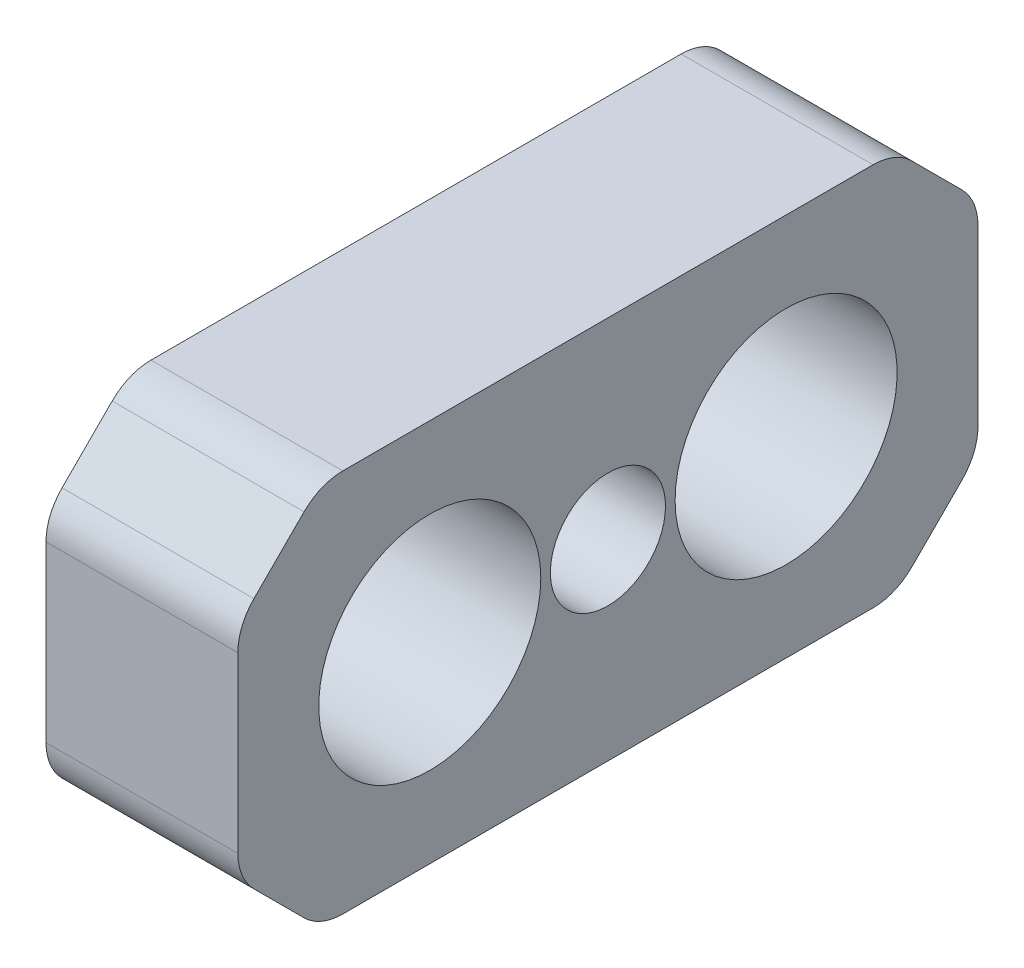
SolidWorks part; units mm, degrees
material "POM Acetal Copolymer"
ref_plane "Front Plane" through (0, 0, 0) normal (0, 0, 1) x (1, 0, 0)
ref_plane "Top Plane" through (0, 0, 0) normal (0, 1, 0) x (1, 0, 0)
ref_plane "Right Plane" through (0, 0, 0) normal (1, 0, 0) x (0, 0, -1)
sketch "Sketch1" plane through (0, 0, 0) normal (1, 0, 0) x (0, 0, -1)
  line L0 (0, 0) -> (0, -17.866) construction
  line L2 (13.5, -7) -> (-13.5, -7)
  line L3 (13.5, -7) -> (13.5, 7)
  line L4 (13.5, 7) -> (-13.5, 7)
  line L5 (-13.5, -7) -> (-13.5, 7)
  line L6 (13.5, -7) -> (-13.5, 7) construction
  line L7 (13.5, 7) -> (-13.5, -7) construction
  circle A0 centre (-6.5, 0) radius 4.05
  circle A1 centre (6.5, 0) radius 4.05
  dimension "D1" = 8.1
  dimension "D2" = 13
  dimension "D3" = 7
  dimension "D4" = 7
extrude "Boss-Extrude1" add sketch "Sketch1" along normal blind 7
fillet "Fillet1" [suppressed] radius 7
sketch "Sketch2" plane through (7, 0, 0) normal (1, 0, 0) x (0, 0, -1)
  line L1 (8.1781, -1) -> (-8.1781, -1)
  line L2 (8.1781, -1) -> (8.1781, 1)
  line L3 (8.1781, 1) -> (-8.1781, 1)
  line L4 (-8.1781, -1) -> (-8.1781, 1)
  line L5 (8.1781, -1) -> (-8.1781, 1) construction
  line L6 (8.1781, 1) -> (-8.1781, -1) construction
  point P0 (0, 0)
  dimension "D1" = 2
extrude "Cut-Extrude1" [suppressed] cut sketch "Sketch2" against normal blind 4.5
sketch "Sketch3" plane through (7, 0, 0) normal (1, 0, 0) x (0, 0, -1)
  circle A0 centre (0, 0) radius 2.1
  dimension "D1" = 4.2
extrude "Cut-Extrude4" cut sketch "Sketch3" against normal blind 5
chamfer "Chanfrein1" distance 3 angle 45 4 edges at (3.5, 7, 13.5) (3.5, -7, 13.5) (3.5, -7, -13.5) (3.5, 7, -13.5)
fillet "Congé1" radius 2 8 edges at (3.5, 4, -13.5) (3.5, 7, -10.5) (3.5, -4, -13.5) (3.5, -7, -10.5) (3.5, -7, 10.5) (3.5, -4, 13.5) (3.5, 4, 13.5) (3.5, 7, 10.5)
